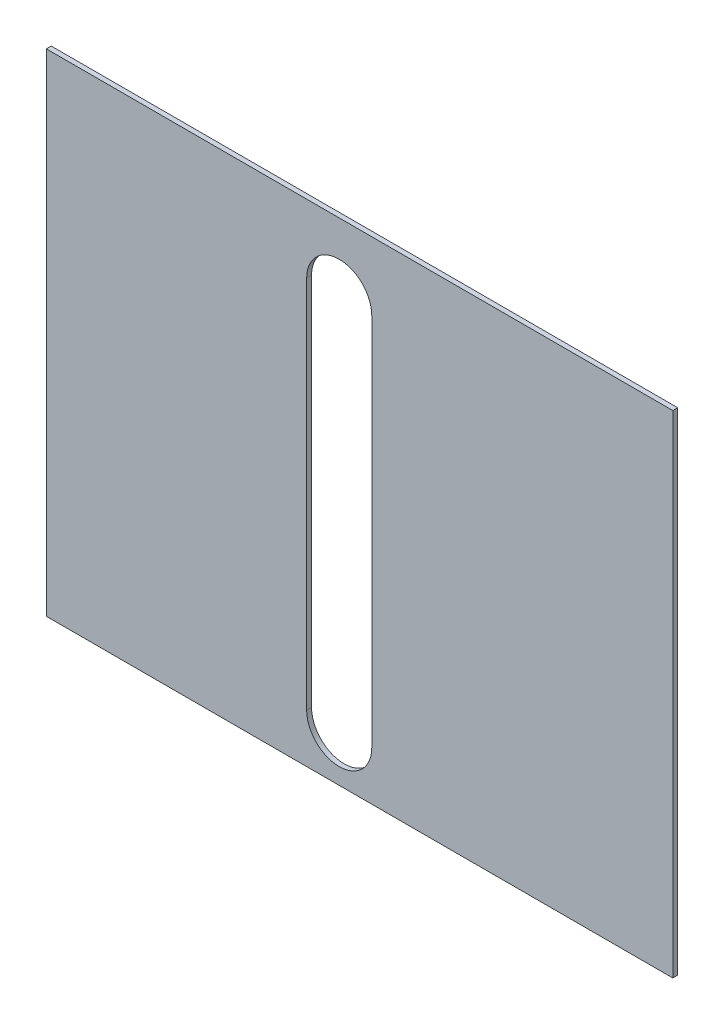
SolidWorks part; units mm, degrees
material "Acrílico (Impacto medio-alto)"
ref_plane "Alzado" through (0, 0, 0) normal (0, 0, 1) x (1, 0, 0)
ref_plane "Planta" through (0, 0, 0) normal (0, 1, 0) x (1, 0, 0)
ref_plane "Vista lateral" through (0, 0, 0) normal (1, 0, 0) x (0, 0, -1)
sketch "Croquis1" plane through (0, 0, 0) normal (0, 0, 1) x (1, 0, 0)
  line L0 (180, 30) -> (180, 260) construction
  line L1 (0, 0) -> (385, 0)
  line L2 (0, 0) -> (0, 302)
  line L3 (0, 302) -> (385, 302)
  line L4 (385, 0) -> (385, 302)
  line L5 (160, 30) -> (160, 260)
  line L6 (200, 30) -> (200, 260)
  arc A0 (160, 30) -> (200, 30) centre (180, 30) ccw
  arc A1 (200, 260) -> (160, 260) centre (180, 260) ccw
  point P7 (180, 145)
  dimension "D3" = 180
  dimension "D1" = 302
  dimension "D2" = 385
  dimension "D4" = 30
  dimension "D5" = 230
extrude "Saliente-Extruir1" add sketch "Croquis1" along normal blind 3
